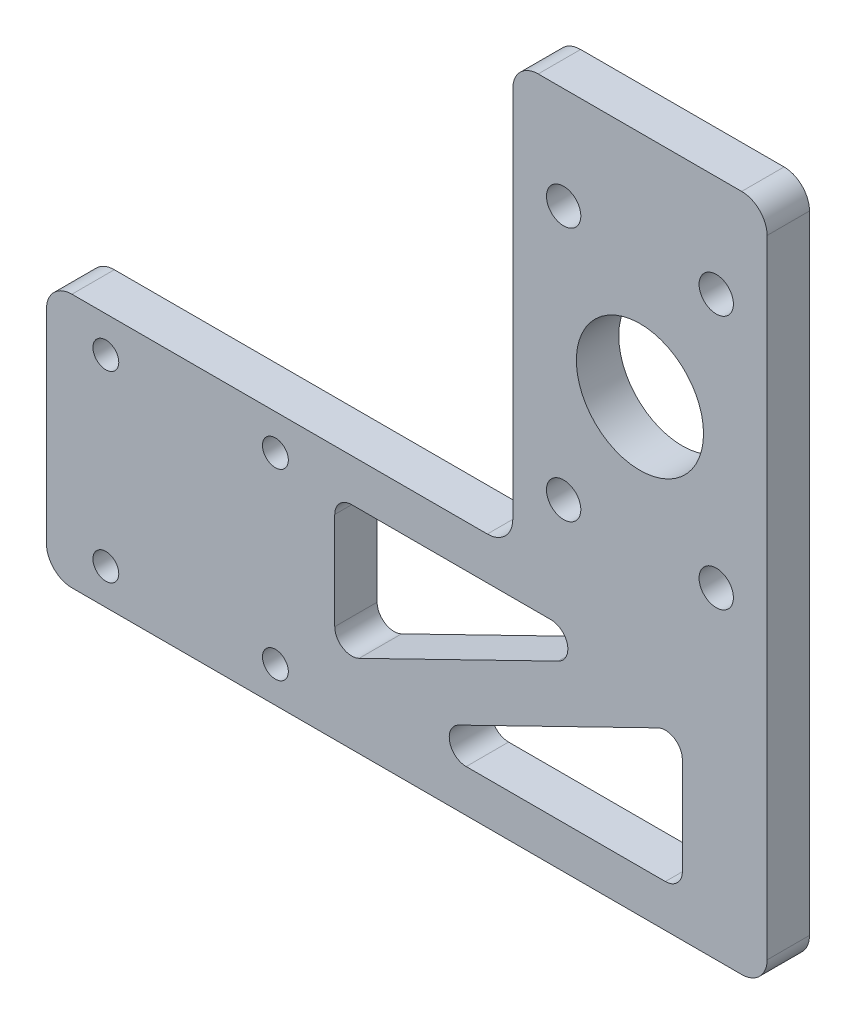
SolidWorks part; units mm, degrees
material "Thornel Mat VMA"
ref_plane "前视基准面" through (0, 0, 0) normal (0, 0, 1) x (1, 0, 0)
ref_plane "上视基准面" through (0, 0, 0) normal (0, 1, 0) x (1, 0, 0)
ref_plane "右视基准面" through (0, 0, 0) normal (1, 0, 0) x (0, 0, -1)
other "Configuration Table"
sketch "草图1" plane through (0, 0, 0) normal (0, 0, 1) x (1, 0, 0)
  line L0 (0, 0) -> (-55, 0)
  line L1 (-55, 0) -> (-55, -30)
  line L2 (-55, -30) -> (30, -30)
  line L3 (30, -30) -> (30, 50)
  line L4 (30, 50) -> (0, 50)
  line L5 (0, 50) -> (0, 0)
  dimension "D1" = 30
  dimension "D2" = 30
  dimension "D3" = 50
  dimension "D4" = 55
extrude "凸台-拉伸1" add sketch "草图1" along normal blind 5
sketch "草图3" plane through (0, 0, 0) normal (0, 0, -1) x (-1, 0, 0)
  circle A0 centre (-24, 38) radius 2.025
  circle A1 centre (-6, 38) radius 2.025
  circle A2 centre (-24, 8) radius 2.025
  circle A3 centre (-6, 8) radius 2.025
  circle A4 centre (-24, 38) radius 2.025 construction
  circle A5 centre (-6, 38) radius 2.025 construction
  circle A6 centre (-24, 8) radius 2.025 construction
  circle A7 centre (-6, 8) radius 2.025 construction
  dimension "D1" = 4.05
extrude "切除-拉伸1" cut sketch "草图3" against normal through all both
fillet "圆角1" radius 3 6 edges at (30, 50, 2.5) (30, -30, 2.5) (-55, -30, 2.5) (-55, 0, 2.5) (0, 0, 2.5) (0, 50, 2.5)
sketch "草图4" plane through (0, 0, 5) normal (0, 0, 1) x (1, 0, 0)
  line L0 (-52, -30) -> (27, -30) construction
  line L1 (-55, -3) -> (-55, -27) construction
  line L3 (-48, -25.8) -> (-28, -25.8) construction
  line L4 (-48, -25.8) -> (-48, -4.2) construction
  line L5 (-48, -4.2) -> (-28, -4.2) construction
  line L6 (-28, -25.8) -> (-28, -4.2) construction
  circle A0 centre (-48, -25.8) radius 1.525
  circle A4 centre (-48, -4.2) radius 1.525
  circle A5 centre (-28, -4.2) radius 1.525
  circle A6 centre (-28, -25.8) radius 1.525
  dimension "D1" = 3.05
  dimension "D2" = 4.2
  dimension "D3" = 7
  dimension "D4" = 20
  dimension "D5" = 21.6
extrude "切除-拉伸2" cut sketch "草图4" against normal through all both
sketch "草图7" plane through (0, 0, 5) normal (0, 0, 1) x (1, 0, 0)
  line L0 (30, -27) -> (30, 47) construction
  line L1 (-21, -5) -> (20, -5)
  line L2 (-21, -5) -> (-21, -25)
  line L3 (-21, -25) -> (20, -25)
  line L4 (20, -5) -> (20, -25)
  line L5 (-3, 0) -> (-52, 0) construction
  line L6 (-52, -30) -> (27, -30) construction
  line L7 (-21, -25) -> (20, -5)
  line L8 (-19.6847, -27.6963) -> (21.3153, -7.6963)
  line L9 (-22.3153, -22.3037) -> (18.6847, -2.3037)
  circle A0 centre (-28, -25.8) radius 1.525 construction
  dimension "D2" = 7
  dimension "D1" = 10
  dimension "D3" = 5
  dimension "D4" = 5
  dimension "D5" = 3
  dimension "D6" = 3
extrude "切除-拉伸3" cut sketch "草图7" against normal through all contours L2 L9 L1 | L8 L3 L4
fillet "圆角2" radius 2 6 edges at (20, -25, 2.5) (-14.1573, -25, 2.5) (20, -8.3379, 2.5) (13.1573, -5, 2.5) (-21, -21.6621, 2.5) (-21, -5, 2.5)
sketch "草图8" plane through (0, 0, 5) normal (0, 0, 1) x (1, 0, 0)
  line L1 (6, 38) -> (24, 38) construction
  line L2 (6, 38) -> (6, 8) construction
  line L3 (6, 8) -> (24, 8) construction
  line L4 (24, 38) -> (24, 8) construction
  circle A0 centre (15, 23) radius 7.5
  point P8 (15, 8)
  point P9 (24, 23)
  dimension "D1" = 15
extrude "切除-拉伸4" cut sketch "草图8" against normal up to surface (5 mm away) up to face at (-11.4429, -10.7587, 0)
